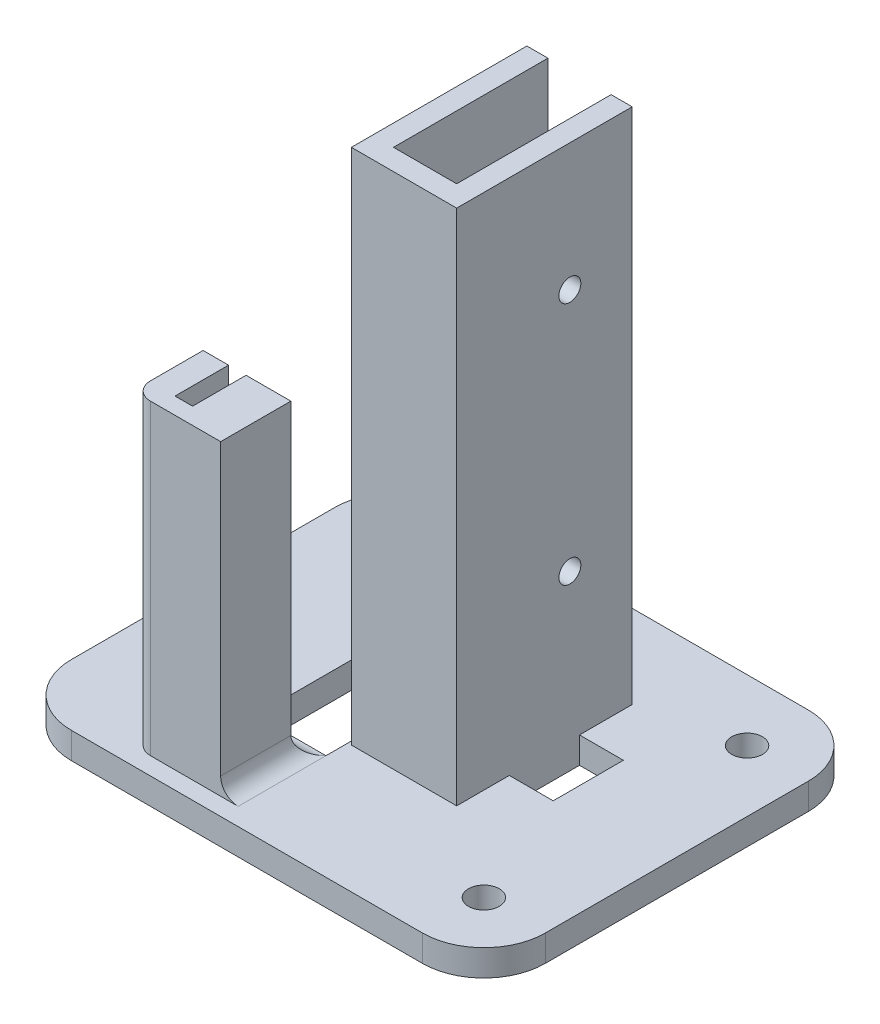
SolidWorks part; units mm, degrees
ref_plane "Alzado" through (0, 0, 0) normal (0, 0, 1) x (1, 0, 0)
ref_plane "Planta" through (0, 0, 0) normal (0, 1, 0) x (1, 0, 0)
ref_plane "Vista lateral" through (0, 0, 0) normal (1, 0, 0) x (0, 0, -1)
sketch "Croquis1" plane through (0, 0, 0) normal (0, 1, 0) x (1, 0, 0)
  line L1 (7, 0) -> (47, 0)
  line L2 (0, 7) -> (0, 37)
  line L3 (7, 44) -> (47, 44)
  line L4 (54, 7) -> (54, 37)
  arc A0 (7, 0) -> (0, 7) centre (7, 7) cw
  arc A1 (47, 0) -> (54, 7) centre (47, 7) ccw
  arc A2 (47, 44) -> (54, 37) centre (47, 37) cw
  arc A3 (0, 37) -> (7, 44) centre (7, 37) cw
  point P7 (0, 0)
  dimension "D3" = 7
  dimension "D1" = 54
  dimension "D2" = 44
extrude "Saliente-Extruir1" add sketch "Croquis1" along normal blind 3
sketch "Croquis2" plane through (0, 3, 0) normal (0, 1, 0) x (1, 0, 0)
  line L0 (41.4, 28.5) -> (36.4, 20.5) construction
  line L1 (36.4, 28.5) -> (41.4, 28.5)
  line L2 (36.4, 28.5) -> (36.4, 20.5)
  line L3 (36.4, 20.5) -> (41.4, 20.5)
  line L4 (41.4, 28.5) -> (41.4, 20.5)
  line L5 (47, 44) -> (7, 44) construction
  line L6 (54, 7) -> (54, 37) construction
  point P4 (38.9, 24.5)
  dimension "D1" = 19.5
  dimension "D2" = 15.1
  dimension "D3" = 8
  dimension "D4" = 5
extrude "Cortar-Extruir1" cut sketch "Croquis2" against normal up to next
sketch "Croquis3" plane through (0, 3, 0) normal (0, 1, 0) x (1, 0, 0)
  line L0 (0, 37) -> (0, 7) construction
  line L1 (12, 34) -> (22, 34)
  line L2 (12, 34) -> (12, 42)
  line L3 (12, 42) -> (22, 42)
  line L4 (22, 34) -> (22, 42)
  line L5 (12, 10) -> (22, 10)
  line L6 (12, 10) -> (12, 2)
  line L7 (12, 2) -> (22, 2)
  line L8 (22, 10) -> (22, 2)
  line L9 (7, 0) -> (47, 0) construction
  line L10 (47, 44) -> (7, 44) construction
  dimension "D1" = 12
  dimension "D2" = 10
  dimension "D3" = 2
  dimension "D4" = 2
  dimension "D5" = 8
  dimension "D6" = 8
extrude "Saliente-Extruir2" add sketch "Croquis3" along normal blind 35
sketch "Croquis4" plane through (0, 38, 0) normal (0, 1, 0) x (1, 0, 0)
  line L7 (14.9, 10.5941) -> (14.9, 3.9)
  line L8 (14.9, 3.9) -> (16.9, 3.9)
  line L9 (16.9, 3.9) -> (16.9, 10.1013)
  line L10 (14.9, 10.5941) -> (14.9, 3.9)
  line L11 (14.9, 3.9) -> (16.9, 3.9)
  line L12 (16.9, 3.9) -> (16.9, 10.1013)
  line L16 (16.9, 17.8987) -> (16.9, 40.1)
  line L17 (16.9, 40.1) -> (14.9, 40.1)
  line L18 (14.9, 40.1) -> (14.9, 17.4059)
  line L19 (16.9, 17.8987) -> (16.9, 40.1)
  line L20 (16.9, 40.1) -> (14.9, 40.1)
  line L21 (14.9, 40.1) -> (14.9, 17.4059)
  arc A2 (14.9, 10.5941) -> (16.9, 10.1013) centre (16.8, 14) ccw
  arc A3 (14.9, 10.5941) -> (16.9, 10.1013) centre (16.8, 14) ccw
  arc A5 (16.9, 17.8987) -> (14.9, 17.4059) centre (16.8, 14) ccw
  arc A6 (16.9, 17.8987) -> (14.9, 17.4059) centre (16.8, 14) ccw
  dimension "D1" = 0.1
  dimension "D2" = 0.1
extrude "Cortar-Extruir2" cut sketch "Croquis4" against normal blind 12
fillet "Redondeo1" radius 2 2 edges at (12, 20.5, -2) (12, 20.5, -42)
fillet "Redondeo2" radius 2 4 edges at (17, 3, -10) (22, 3, -6) (22, 3, -38) (17, 3, -34)
sketch "Croquis5" plane through (0, 3, 0) normal (0, 1, 0) x (1, 0, 0)
  line L0 (36.4, 34.5) -> (36.4, 14.5)
  line L1 (36.4, 14.5) -> (24.4, 14.5)
  line L2 (24.4, 14.5) -> (24.4, 34.5)
  line L3 (24.4, 34.5) -> (26.8, 34.5)
  line L4 (26.8, 34.5) -> (26.8, 16.9)
  line L5 (26.8, 16.9) -> (34, 16.9)
  line L6 (34, 16.9) -> (34, 34.5)
  line L7 (34, 34.5) -> (36.4, 34.5)
  line L8 (41.4, 20.5) -> (41.4, 28.5) construction
  point P9 (41.4, 24.5)
  point P12 (36.4, 24.5)
  dimension "D1" = 20
  dimension "D2" = 2.4
  dimension "D3" = 2.4
  dimension "D4" = 2.4
  dimension "D5" = 12
extrude "Saliente-Extruir3" add sketch "Croquis5" along normal blind 59
sketch "Croquis6" plane through (36.4, 0, 0) normal (1, 0, 0) x (0, 0, -1)
  line L0 (34.5, 62) -> (34.5, 3) construction
  line L1 (42, 3) -> (32, 3) construction
  line L2 (28.5, 3) -> (34.5, 3) construction
  circle A0 centre (27.4, 47.5) radius 1.25
  circle A1 centre (27.4, 19.7) radius 1.25
  point P4 (0, 0)
  dimension "D1" = 7.1
  dimension "D3" = 44.5
  dimension "D4" = 2.5
  dimension "D2" = 16.7
extrude "Cortar-Extruir3" cut sketch "Croquis6" against normal up to next
sketch "Croquis7" plane through (0, 3, 0) normal (0, 1, 0) x (1, 0, 0)
  line L0 (0, 37) -> (0, 7) construction
  line L1 (16, 32) -> (24, 32)
  line L2 (16, 32) -> (16, 12)
  line L3 (16, 12) -> (24, 12)
  line L4 (24, 32) -> (24, 12)
  circle A0 centre (4, 22) radius 1.75
  circle A1 centre (47, 37) radius 1.75
  circle A2 centre (47, 7) radius 1.75
  arc A3 (54, 37) -> (47, 44) centre (47, 37) ccw construction
  arc A4 (47, 0) -> (54, 7) centre (47, 7) ccw construction
  point P14 (0, 22)
  dimension "D2" = 4
  dimension "D3" = 3.5
  dimension "D1" = 8
extrude "Cortar-Extruir4" cut sketch "Croquis7" against normal up to next
